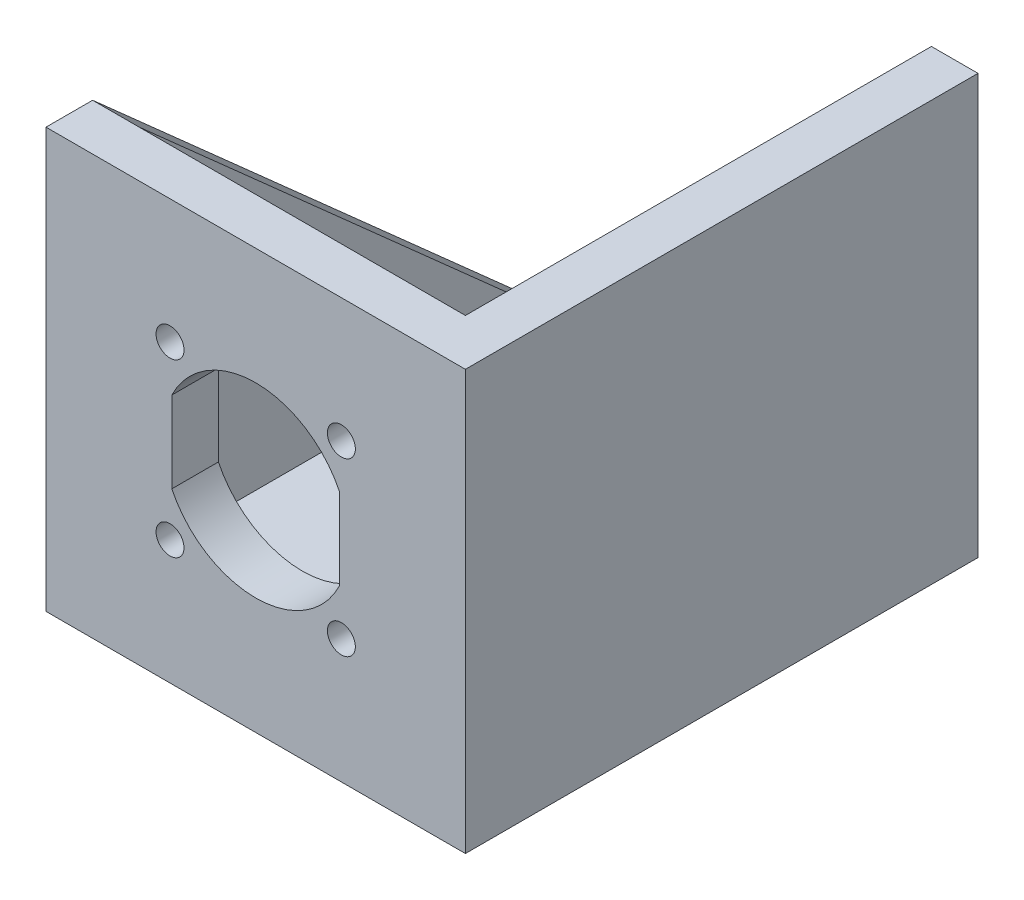
SolidWorks part; units mm, degrees
ref_plane "Plan de face" through (0, 0, 0) normal (0, 0, 1) x (1, 0, 0)
ref_plane "Plan de dessus" through (0, 0, 0) normal (0, 1, 0) x (1, 0, 0)
ref_plane "Plan de droite" through (0, 0, 0) normal (1, 0, 0) x (0, 0, -1)
sketch "Esquisse1" plane through (0, 0, 0) normal (0, 0, 1) x (1, 0, 0)
  line L0 (45, 0) -> (0, 45) construction
  line L1 (0, 0) -> (45, 0)
  line L2 (0, 0) -> (0, 45)
  line L3 (0, 45) -> (45, 45)
  line L4 (45, 0) -> (45, 45)
  line L5 (0, 0) -> (45, 45) construction
  line L6 (22.5, 45) -> (22.5, 0) construction
  line L7 (13.5, 26.8589) -> (13.5, 18.1411)
  line L8 (45, 22.5) -> (0, 22.5) construction
  line L9 (31.5, 26.8589) -> (31.5, 18.1411)
  arc A0 (13.5, 18.1411) -> (31.5, 18.1411) centre (22.5, 22.5) ccw
  circle A1 centre (31.6924, 31.6924) radius 1.5
  circle A2 centre (31.6924, 13.3076) radius 1.5
  circle A3 centre (13.3076, 13.3076) radius 1.5
  circle A4 centre (13.3076, 31.6924) radius 1.5
  arc A5 (31.5, 26.8589) -> (13.5, 26.8589) centre (22.5, 22.5) ccw
  dimension "D3" = 20
  dimension "D5" = 3
  dimension "D1" = 45
  dimension "D2" = 45
  dimension "D4" = 13
  dimension "D6" = 9
extrude "Extrusion1" add sketch "Esquisse1" along normal blind 5
sketch "Esquisse2" plane through (0, 0, 5) normal (0, 0, 1) x (1, 0, 0)
  line L0 (45, 0) -> (45, 45) construction
  line L1 (0, 0) -> (45, 0)
  line L2 (0, 0) -> (0, 5)
  line L3 (0, 5) -> (45, 5)
  line L4 (45, 0) -> (45, 5)
  dimension "D1" = 5
extrude "Extrusion2" add sketch "Esquisse2" along normal blind 95
sketch "Esquisse3" plane through (45, 0, 0) normal (1, 0, 0) x (0, 0, -1)
  line L0 (-5, 5) -> (-5, 45)
  line L1 (-5, 45) -> (-50, 5)
  line L2 (-100, 5) -> (-5, 5) construction
  line L3 (-50, 5) -> (-5, 5)
  dimension "D1" = 45
extrude "Extrusion3" add sketch "Esquisse3" against normal blind 5
sketch "Esquisse4" plane through (0, 0, 0) normal (-1, 0, 0) x (0, 0, 1)
  line L0 (5, 5) -> (5, 45)
  line L1 (5, 45) -> (100, 45)
  line L2 (100, 45) -> (100, 5)
  line L3 (100, 5) -> (5, 5)
extrude "Extrusion4" add sketch "Esquisse4" against normal blind 5
sketch "Esquisse5" plane through (0, 0, 0) normal (-1, 0, 0) x (0, 0, 1)
  line L0 (100, 45) -> (100, 0) construction
  line L1 (0, 0) -> (100, 0)
  line L2 (0, 0) -> (0, 5)
  line L3 (0, 5) -> (100, 5)
  line L4 (100, 0) -> (100, 5)
  dimension "D1" = 5
extrude "Extrusion5" add sketch "Esquisse5" along normal blind 40
sketch "Esquisse6" plane through (0, 0, 100) normal (0, 0, 1) x (1, 0, 0)
  line L0 (0, 5) -> (0, 45)
  line L1 (0, 45) -> (-40, 45)
  line L2 (-40, 45) -> (-40, 5)
  line L3 (-40, 5) -> (0, 5)
extrude "Extrusion6" add sketch "Esquisse6" against normal blind 5
sketch "Esquisse7" plane through (-40, 0, 0) normal (-1, 0, 0) x (0, 0, 1)
  line L0 (95, 5) -> (95, 45)
  line L1 (95, 45) -> (50, 5)
  line L2 (95, 5) -> (0, 5) construction
  line L3 (50, 5) -> (95, 5)
  dimension "D1" = 45
extrude "Extrusion7" add sketch "Esquisse7" against normal blind 5
sketch "Esquisse8" plane through (0, 0, 100) normal (0, 0, 1) x (1, 0, 0)
  line L0 (5, 5) -> (5, 0) construction
  line L1 (-40, 0) -> (45, 0) construction
  line L2 (5, 0) -> (-40, 45) construction
  line L3 (-40, 22.5) -> (5, 22.5) construction
  line L5 (-26.5, 18.1411) -> (-26.5, 26.8589)
  line L6 (-40, 0) -> (-40, 45) construction
  line L7 (5, 5) -> (5, 45) construction
  line L8 (5, 45) -> (-40, 0) construction
  line L9 (-8.5, 18.1411) -> (-8.5, 26.8589)
  line L10 (5, 45) -> (-40, 45) construction
  line L11 (-17.5, 45) -> (-17.5, 0) construction
  arc A0 (-26.5, 18.1411) -> (-8.5, 18.1411) centre (-17.5, 22.5) ccw
  circle A1 centre (-26.6924, 31.6924) radius 1.5
  circle A2 centre (-26.6924, 13.3076) radius 1.5
  circle A3 centre (-8.3076, 13.3076) radius 1.5
  circle A4 centre (-8.3076, 31.6924) radius 1.5
  arc A5 (-8.5, 26.8589) -> (-26.5, 26.8589) centre (-17.5, 22.5) ccw
  dimension "D1" = 20
  dimension "D2" = 3
  dimension "D3" = 13
  dimension "D4" = 9
extrude "Enlèv. mat.-Extru.1" cut sketch "Esquisse8" against normal up to next
sketch "Esquisse9" plane through (0, 5, 0) normal (0, 1, 0) x (-1, 0, 0)
  line L0 (-45, 100) -> (-5, 100) construction
  line L1 (-45, 100) -> (-45, 50) construction
  line L2 (40, 0) -> (0, 0) construction
  line L3 (40, 50) -> (40, 0) construction
  circle A0 centre (-40, 95) radius 1.5
  circle A1 centre (-10, 95) radius 1.5
  circle A2 centre (35, 5) radius 1.5
  circle A3 centre (5, 5) radius 1.5
  circle A4 centre (-40, 55) radius 1.5
  circle A5 centre (35, 45) radius 1.5
  dimension "D1" = 3
  dimension "D2" = 3
  dimension "D4" = 5
  dimension "D6" = 35
  dimension "D7" = 5
  dimension "D9" = 3
  dimension "D10" = 3
  dimension "D13" = 3
  dimension "D16" = 3
  dimension "D17" = 45
  dimension "D18" = 5
  dimension "D3" = 5
  dimension "D5" = 5
  dimension "D8" = 5
  dimension "D11" = 35
  dimension "D12" = 5
  dimension "D14" = 5
  dimension "D15" = 45
extrude "Enlèv. mat.-Extru.2" cut sketch "Esquisse9" against normal up to next
sketch "Esquisse10" plane through (0, 0, 0) normal (0, 0, -1) x (-1, 0, 0)
  line L1 (-45, 0) -> (43.9359, 0)
  line L2 (-45, 0) -> (-45, 49.0146)
  line L3 (-45, 49.0146) -> (43.9359, 49.0146)
  line L4 (43.9359, 0) -> (43.9359, 49.0146)
extrude "Enlèv. mat.-Extru.3" cut sketch "Esquisse10" against normal blind 45
sketch "Esquisse11" plane through (45, 0, 0) normal (1, 0, 0) x (0, 0, -1)
  line L1 (-100, 0) -> (-37.8572, 0)
  line L2 (-100, 0) -> (-100, 38.0285)
  line L3 (-100, 38.0285) -> (-37.8572, 38.0285)
  line L4 (-37.8572, 0) -> (-37.8572, 38.0285)
extrude "Enlèv. mat.-Extru.4" cut sketch "Esquisse11" against normal blind 40
sketch "Esquisse12" plane through (0, 5, 0) normal (0, 1, 0) x (-1, 0, 0)
  circle A0 centre (19.8901, 72.4969) radius 2
  dimension "D1" = 4
extrude "Enlèv. mat.-Extru.5" cut sketch "Esquisse12" against normal up to next
